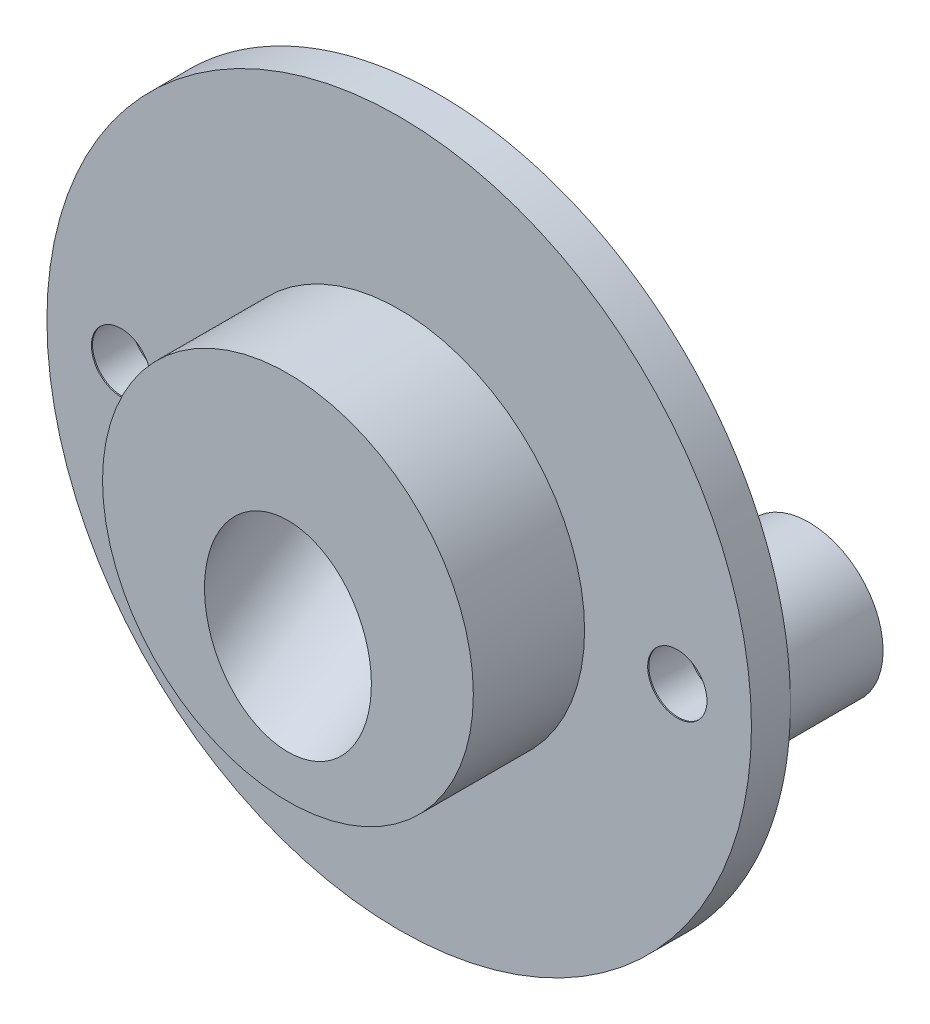
SolidWorks part; units mm, degrees
ref_plane "Plan de face" through (0, 0, 0) normal (0, 0, 1) x (1, 0, 0)
ref_plane "Plan de dessus" through (0, 0, 0) normal (0, 1, 0) x (1, 0, 0)
ref_plane "Plan de droite" through (0, 0, 0) normal (1, 0, 0) x (0, 0, -1)
sketch "Esquisse1" plane through (0, 0, 0) normal (0, 0, 1) x (1, 0, 0)
  circle A0 centre (0, 0) radius 19
  dimension "D1" = 38
extrude "Boss.-Extru.1" add sketch "Esquisse1" along normal blind 2.1
sketch "Esquisse2" plane through (0, 0, 2.1) normal (0, 0, 1) x (1, 0, 0)
  circle A0 centre (0, 0) radius 10
  dimension "D1" = 20
extrude "Boss.-Extru.2" add sketch "Esquisse2" along normal blind 6
sketch "Esquisse3" plane through (0, 0, 0) normal (1, 0, 0) x (0, 0, -1)
  line L0 (0, 0) -> (7.5, 0) construction
  line L1 (7.5, 0) -> (0, -11.25)
  line L2 (0, -11.25) -> (0, 0)
  line L3 (7.5, 0) -> (0, 0)
  dimension "D1" = 7.5
  dimension "D2" = 11.25
revolve "Révolution1" add sketch "Esquisse3" angle 360 about L0
sketch3d "Esquisse3D1"
  line L0 (0, 0, -7.5) -> (0, 11.25, 0) construction
  line L1 (0, 0, -7.5) -> (0, 11.25, -7.5) construction
  line L2 (0, 11.25, -7.5) -> (0, 11.25, 0) construction
  circle A5 centre (0, 0, 0) radius 11.25 construction
  point P10 (0, 0, 11.25)
ref_plane "Plan1" through (0, 3.4615, -5.1923) normal (0, 0.5547, -0.8321) x (0, 0.8321, 0.5547)
sketch "Esquisse4" plane through (0, 3.4615, -5.1923) normal (0, 0.5547, -0.8321) x (0, 0.8321, 0.5547)
  line L0 (-4.1603, 0) -> (9.3606, 0) construction
  line L1 (-4.1603, 0) -> (9.3606, 0) construction
  circle A0 centre (2.6002, 0) radius 4.5
  dimension "D1" = 9
extrude "Enlèv. mat.-Extru.1" cut sketch "Esquisse4" against normal blind 21
sketch "Esquisse5" plane through (0, 3.4615, -5.1923) normal (0, 0.5547, -0.8321) x (0, 0.8321, 0.5547)
  circle A0 centre (2.6002, 0) radius 4.5 construction
  circle A1 centre (2.6002, 0) radius 4.5 construction
  circle A2 centre (2.6002, 0) radius 6
  dimension "D1" = 12
extrude "Enlèv. mat.-Extru.2" cut sketch "Esquisse5" against normal blind 7.2
sketch "Esquisse6" plane through (0, 0, 0) normal (0, 1, 0) x (1, 0, 0)
  line L0 (11.25, 0) -> (0, 7.5) construction
  line L3 (0, 7.5) -> (-11.25, 0) construction
  line L4 (2.7481, 5.6679) -> (0, 7.5)
  line L5 (0, 7.5) -> (-2.7481, 5.6679)
  line L6 (11.25, 0) -> (0, 7.5) construction
  arc A0 (2.7481, 5.6679) -> (-2.7481, 5.6679) centre (0, 1.5458) ccw
  point P12 (0, 6.5)
  dimension "D2" = 1
extrude "Enlèv. mat.-Extru.3" cut sketch "Esquisse6" along normal blind 4.2 and the other way blind 10
fillet "Congé1" radius 4 1 edges at (-0.1111, -1.4978, -6.4988)
sketch "Esquisse7" plane through (0, 0, 0) normal (0, 0, -1) x (-1, 0, 0)
  line L0 (-19, 0) -> (19, 0) construction
  line L1 (0, 0) -> (0, 7.0156) construction
  circle A0 centre (0, 0) radius 19 construction
  circle A1 centre (-15, 0) radius 1.6
  circle A2 centre (15, 0) radius 1.6
  dimension "D2" = 3.2
  dimension "D1" = 30
extrude "Enlèv. mat.-Extru.4" cut sketch "Esquisse7" against normal blind 4.2
fillet "Congé2" radius 4 1 edges at (11.25, 0, 0)
sketch "Esquisse8" plane through (0, 0, 0) normal (0, 1, 0) x (1, 0, 0)
  line L0 (12.4611, 0) -> (-12.4611, 0) construction
  line L1 (12.4611, 0) -> (-12.4611, 0)
  line L2 (12.4611, 0) -> (-12.4611, 0)
  line L3 (12.4611, 0) -> (12.4611, 11.3274)
  line L4 (-12.4611, 0) -> (-12.4611, 11.3274)
  line L5 (12.4611, 11.3274) -> (-12.4611, 11.3274)
  line L6 (-12.4611, 5.6637) -> (12.4611, 5.6637) construction
  line L7 (0, 0) -> (0, 11.3274) construction
  point P197 (0, 5.6637)
extrude "Enlèv. mat.-Extru.5" cut sketch "Esquisse8" against normal mid plane 50 contours L3 L5 L4 L1
sketch "Esquisse9" plane through (0, 0, 0) normal (0, 0, -1) x (-1, 0, 0)
  circle A0 centre (-15, 0) radius 4
  circle A1 centre (15, 0) radius 4
  circle A2 centre (0, 0) radius 19 construction
  circle A3 centre (15, 0) radius 1.6 construction
  circle A4 centre (-15, 0) radius 1.6 construction
  circle A5 centre (15, 0) radius 1.6
  circle A6 centre (-15, 0) radius 1.6
extrude "Boss.-Extru.4" add sketch "Esquisse9" along normal blind 5
hole_wizard "Chambrage pour vis à tête ronde bombée M21" positions "Esquisse3D2" profile "Esquisse10" counterbore size "M2" standard "Ansi Metric"
sketch3d "Esquisse3D2"
  line L0 (15, 0, 2.1) -> (15, 0, -5) construction
  line L1 (-15, 0, 2.1) -> (-15, 0, -5) construction
  point P0 (15, 0, -5)
  point P4 (-15, 0, -5)
sketch "Esquisse10" plane through (15, 0, -5) normal (1, 0, 0) x (0, 1, 0)
  line L0 (0, 0) -> (0, 8)
  line L1 (0, 8) -> (1.75, 6.9485)
  line L2 (1.75, 6.9485) -> (1.75, 4.8)
  line L3 (1.75, 4.8) -> (2.175, 4.8)
  line L4 (2.175, 4.8) -> (2.175, 0)
  line L5 (2.175, 0) -> (0, 0)
  line L10 (0, 8) -> (-1.75, 6.9485) construction
  line L11 (0, -6.35) -> (0, 107.95) construction
  dimension "Diamètre du perçage" = 3.5
  dimension "Profondeur du perçage" = 8
  dimension "Diamètre du chambrage" = 4.35
  dimension "Profondeur du chambrage" = 4.8
  dimension "Angle de pointe" = 118
sketch "Esquisse11" plane through (0, 0, 0) normal (0, 0, -1) x (-1, 0, 0)
  arc A0 (-19, 0) -> (19, 0) centre (0, 0) ccw construction
  arc A1 (19, 0) -> (-19, 0) centre (0, 0) ccw construction
  arc A2 (-19, 0) -> (19, 0) centre (0, 0) ccw
  arc A3 (19, 0) -> (-19, 0) centre (0, 0) ccw
  circle A4 centre (15, 0) radius 4 construction
  circle A5 centre (-15, 0) radius 4 construction
  circle A6 centre (15, 0) radius 4
  circle A7 centre (-15, 0) radius 4
